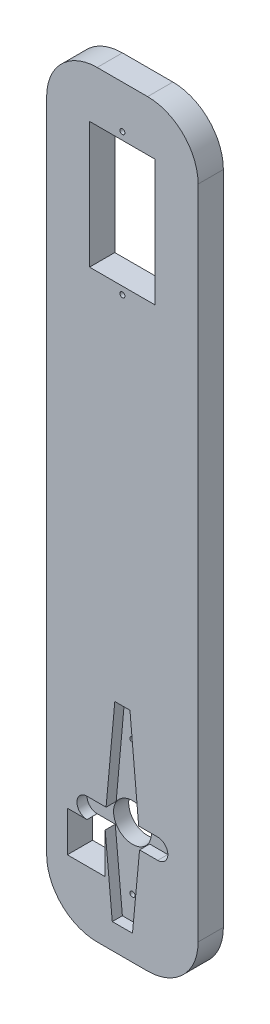
SolidWorks part; units mm, degrees
ref_plane "Přední rovina" through (0, 0, 0) normal (0, 0, 1) x (1, 0, 0)
ref_plane "Horní rovina" through (0, 0, 0) normal (0, 1, 0) x (1, 0, 0)
ref_plane "Pravá rovina" through (0, 0, 0) normal (1, 0, 0) x (0, 0, -1)
sketch "Skica1" plane through (0, 0, 0) normal (0, 0, 1) x (1, 0, 0)
  line L1 (0, 0) -> (30, 0)
  line L2 (0, 0) -> (0, 150)
  line L3 (0, 150) -> (30, 150)
  line L4 (30, 0) -> (30, 150)
  dimension "D1" = 150
  dimension "D2" = 30
extrude "Přidat vysunutím1" add sketch "Skica1" along normal blind 5
fillet "Zaoblit1" radius 10 4 edges at (30, 0, 2.5) (0, 0, 2.5) (30, 150, 2.5) (0, 150, 2.5)
sketch "Skica2" plane through (0, 0, 5) normal (0, 0, 1) x (1, 0, 0)
  line L1 (8.5, 140) -> (21.5, 140)
  line L2 (8.5, 140) -> (8.5, 115)
  line L3 (8.5, 115) -> (21.5, 115)
  line L4 (21.5, 140) -> (21.5, 115)
  line L5 (20, 150) -> (10, 150) construction
  point P4 (15, 150)
  point P7 (15, 140)
  dimension "D1" = 13
  dimension "D2" = 25
  dimension "D3" = 10
extrude "Odebrat vysunutím1" cut sketch "Skica2" against normal through all
sketch "Skica3" plane through (0, 0, 5) normal (0, 0, 1) x (1, 0, 0)
  line L0 (21.5, 140) -> (8.5, 140) construction
  line L2 (8.5, 140) -> (8.5, 115) construction
  line L3 (8.5, 127.5) -> (21.5, 127.5) construction
  line L4 (21.5, 115) -> (21.5, 140) construction
  circle A0 centre (15, 141.5) radius 0.5
  circle A1 centre (15, 113.5) radius 0.5
  point P4 (15, 140)
  point P9 (8.5, 127.5)
  dimension "D1" = 1
  dimension "D2" = 14
  dimension "D3" = 28
extrude "Odebrat vysunutím2" cut sketch "Skica3" against normal through all
sketch "Skica4" plane through (0, 0, 5) normal (0, 0, 1) x (1, 0, 0)
  line L0 (11.5, 21) -> (18.5, 21)
  line L1 (18.5, 21) -> (16.5, 43)
  line L3 (13.5, 43) -> (11.5, 21)
  line L4 (13.5, 43) -> (16.5, 43)
  line L5 (11.5, 21) -> (13, 5)
  line L6 (13, 5) -> (17, 5)
  line L7 (17, 5) -> (18.5, 21)
  line L8 (10, 0) -> (20, 0) construction
  line L10 (8, 24) -> (22, 24)
  line L11 (8, 24) -> (8, 20)
  line L12 (8, 20) -> (22, 20)
  line L13 (22, 24) -> (22, 20)
  arc A0 (8, 24) -> (8, 20) centre (8, 22) ccw
  arc A1 (22, 24) -> (22, 20) centre (22, 22) cw
  point P2 (15, 43)
  point P5 (15, 21)
  point P6 (15, 5)
  point P11 (15, 0)
  point P16 (15, 24)
  dimension "D1" = 7
  dimension "D2" = 3
  dimension "D3" = 22
  dimension "D4" = 16
  dimension "D5" = 5
  dimension "D6" = 4
  dimension "D7" = 19
  dimension "D8" = 14
  dimension "D9" = 4
extrude "Odebrat vysunutím3" cut sketch "Skica4" against normal blind 2 contours L12 L5 L6 L7 | L5 L12 L7 L0 | L11 L12 L5 L3 L10 | L10 L3 L0 L1 | L13 L10 L1 L7 L12 | A1 L13 | L11 A0 | L3 L10 L1 L4
sketch "Skica5" plane through (0, 0, 3) normal (0, 0, 1) x (1, 0, 0)
  line L0 (6, 22) -> (24, 22) construction
  line L1 (13.5, 43) -> (16.5, 43) construction
  circle A0 centre (15, 36.2) radius 0.5
  circle A1 centre (15, 9.7) radius 0.5
  arc A2 (8, 24) -> (8, 20) centre (8, 22) ccw construction
  arc A3 (22, 20) -> (22, 24) centre (22, 22) ccw construction
  point P10 (15, 43)
  dimension "D1" = 1
  dimension "D2" = 1
  dimension "D4" = 14.2
  dimension "D3" = 12.3
extrude "Odebrat vysunutím4" cut sketch "Skica5" against normal through all
sketch "Skica6" plane through (0, 0, 3) normal (0, 0, 1) x (1, 0, 0)
  line L0 (6, 22) -> (24, 22) construction
  line L1 (15, 43) -> (15, 5) construction
  line L2 (13.5, 43) -> (16.5, 43) construction
  line L3 (13, 5) -> (17, 5) construction
  circle A0 centre (15, 22) radius 3.75
  arc A1 (8, 24) -> (8, 20) centre (8, 22) ccw construction
  arc A2 (22, 20) -> (22, 24) centre (22, 22) ccw construction
  point P16 (15, 22)
  dimension "D2" = 7.5
  dimension "D1" = 0
extrude "Odebrat vysunutím5" cut sketch "Skica6" against normal through all
sketch "Skica7" plane through (0, 0, 5) normal (0, 0, 1) x (1, 0, 0)
  line L1 (11.5937, 20) -> (4.0937, 20)
  line L2 (11.5937, 20) -> (11.5938, 12)
  line L3 (11.5938, 12) -> (4.0938, 12)
  line L4 (4.0937, 20) -> (4.0938, 12)
  dimension "D1" = 8
  dimension "D2" = 7.5
extrude "Odebrat vysunutím6" cut sketch "Skica7" against normal through all
